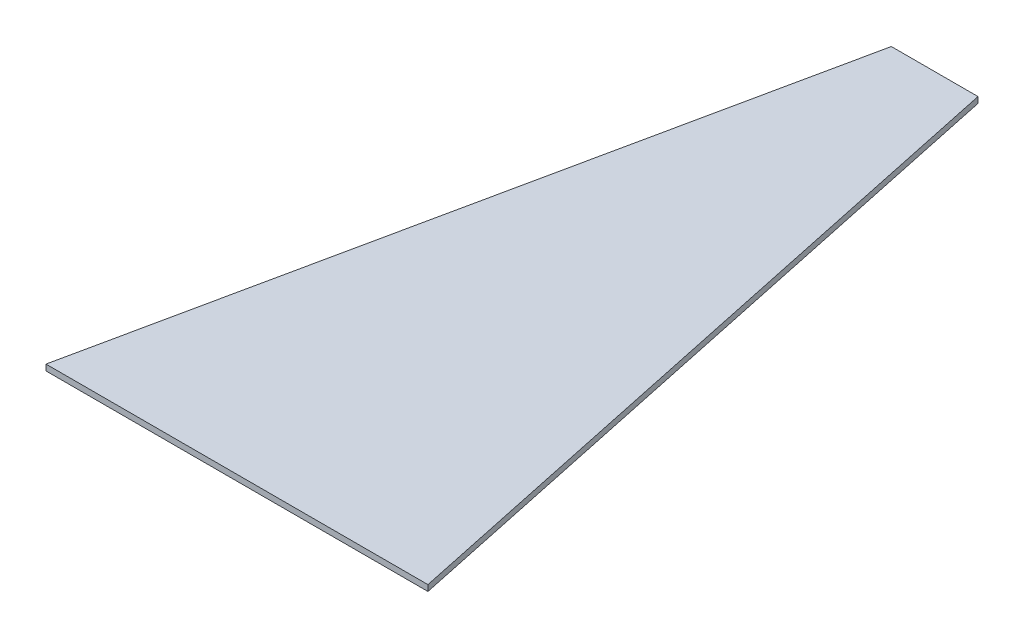
SolidWorks part; units mm, degrees
ref_plane "Plan de face" through (0, 0, 0) normal (0, 0, 1) x (1, 0, 0)
ref_plane "Plan de dessus" through (0, 0, 0) normal (0, 1, 0) x (1, 0, 0)
ref_plane "Plan de droite" through (0, 0, 0) normal (1, 0, 0) x (0, 0, -1)
sketch "Esquisse1" plane through (0, 0, 0) normal (0, 1, 0) x (1, 0, 0)
  line L0 (78.5377, 233.8636) -> (49.4868, 233.8636)
  line L1 (49.4868, 233.8636) -> (0, 0)
  line L2 (0, 0) -> (128.0246, 0)
  line L3 (128.0246, 0) -> (78.5377, 233.8636)
  point P4 (0, 0)
extrude "Boss.-Extru.1" add sketch "Esquisse1" along normal blind 2
